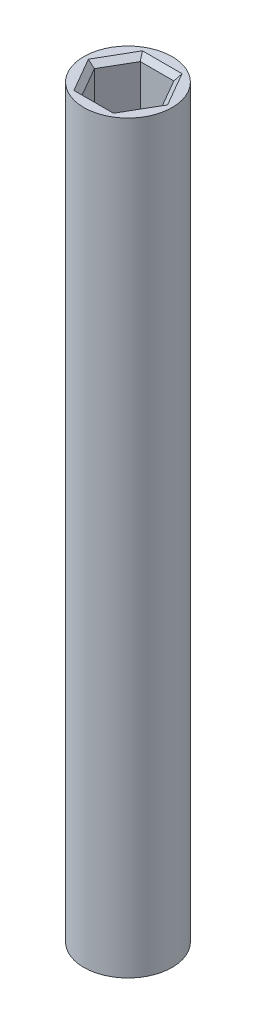
SolidWorks part; units mm, degrees
material "ABS"
ref_plane "Front Plane" through (0, 0, 0) normal (0, 0, 1) x (1, 0, 0)
ref_plane "Top Plane" through (0, 0, 0) normal (0, 1, 0) x (1, 0, 0)
ref_plane "Right Plane" through (0, 0, 0) normal (1, 0, 0) x (0, 0, -1)
sketch "Sketch1" plane through (0, 0, 0) normal (0, 1, 0) x (1, 0, 0)
  circle A0 centre (0, 0) radius 4.25
  dimension "D1" = 8.5
extrude "Boss-Extrude1" add sketch "Sketch1" along normal blind 71.6875
sketch "Sketch2" plane through (0, 71.6875, 0) normal (0, 1, 0) x (1, 0, 0)
  line L1 (1.6166, 2.8) -> (-1.6166, 2.8)
  line L2 (-1.6166, 2.8) -> (-3.2332, 0)
  line L3 (-3.2332, 0) -> (-1.6166, -2.8)
  line L4 (-1.6166, -2.8) -> (1.6166, -2.8)
  line L5 (1.6166, -2.8) -> (3.2332, 0)
  line L6 (3.2332, 0) -> (1.6166, 2.8)
  circle A0 centre (0, 0) radius 2.8 construction
  dimension "D1" = 5.6
extrude "Cut-Extrude1" cut sketch "Sketch2" against normal blind 6.6
chamfer "Chamfer1" distance 0.5 angle 45 6 edges at (0, 71.6875, 2.8) (2.4249, 71.6875, 1.4) (2.4249, 71.6875, -1.4) (0, 71.6875, -2.8) (-2.4249, 71.6875, 1.4) (-2.4249, 71.6875, -1.4)
sketch "Sketch3" plane through (0, 0, 0) normal (0, -1, 0) x (1, 0, 0)
  line L1 (0, 3.2332) -> (-2.8, 1.6166)
  line L2 (-2.8, 1.6166) -> (-2.8, -1.6166)
  line L3 (-2.8, -1.6166) -> (0, -3.2332)
  line L4 (0, -3.2332) -> (2.8, -1.6166)
  line L5 (2.8, -1.6166) -> (2.8, 1.6166)
  line L6 (2.8, 1.6166) -> (0, 3.2332)
  circle A0 centre (0, 0) radius 2.8 construction
  dimension "D1" = 5.6
extrude "Cut-Extrude2" cut sketch "Sketch3" against normal blind 6.6
chamfer "Chamfer2" distance 0.5 angle 45 6 edges at (1.4, 0, 2.4249) (-1.4, 0, 2.4249) (-2.8, 0, 0) (-1.4, 0, -2.4249) (1.4, 0, -2.4249) (2.8, 0, 0)
sketch3d "3DSketch1"
  line L0 (0, 0, 0) -> (0, 71.6875, 0)
